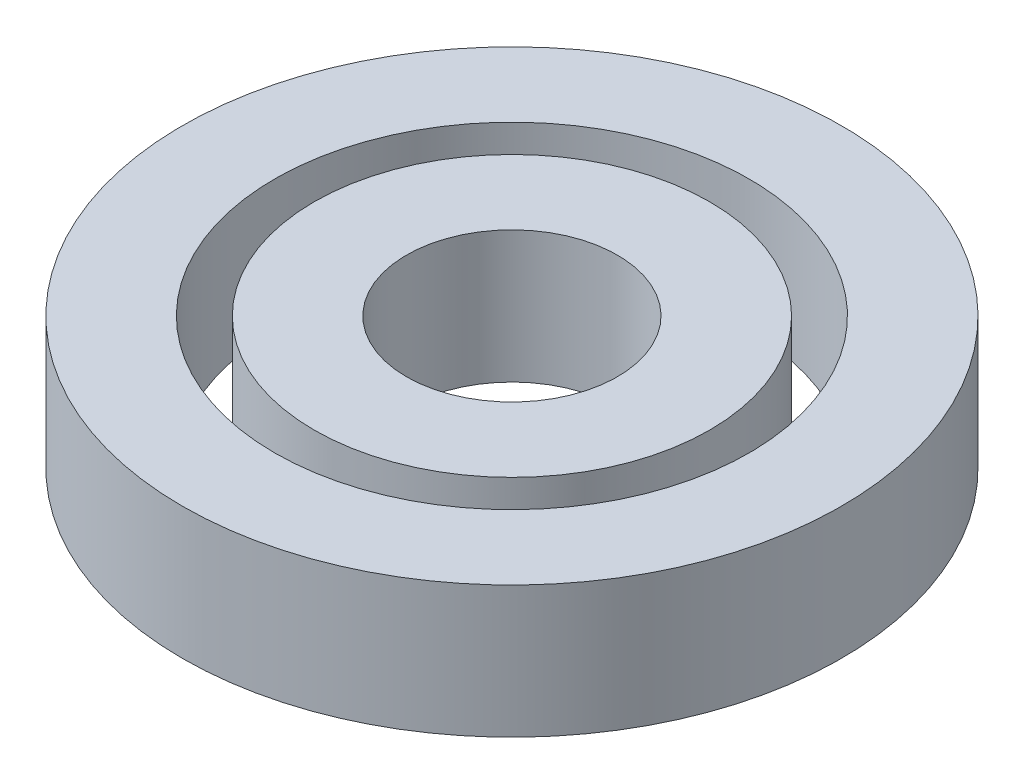
SolidWorks part; units mm, degrees
ref_plane "Front Plane" through (0, 0, 0) normal (0, 0, 1) x (1, 0, 0)
ref_plane "Top Plane" through (0, 0, 0) normal (0, 1, 0) x (1, 0, 0)
ref_plane "Right Plane" through (0, 0, 0) normal (1, 0, 0) x (0, 0, -1)
sketch "Sketch1" plane through (0, 0, 0) normal (0, 1, 0) x (1, 0, 0)
  circle A0 centre (0, 0) radius 4
  circle A1 centre (0, 0) radius 7.5
  dimension "D1" = 8
  dimension "D2" = 15
extrude "Boss-Extrude1" add sketch "Sketch1" along normal blind 5
sketch "Sketch2" plane through (0, 0, 0) normal (0, 1, 0) x (1, 0, 0)
  circle A0 centre (0, 0) radius 9
  circle A1 centre (0, 0) radius 12.5
  dimension "D1" = 18
  dimension "D2" = 25
extrude "Boss-Extrude2" add sketch "Sketch2" along normal blind 5 separate body
